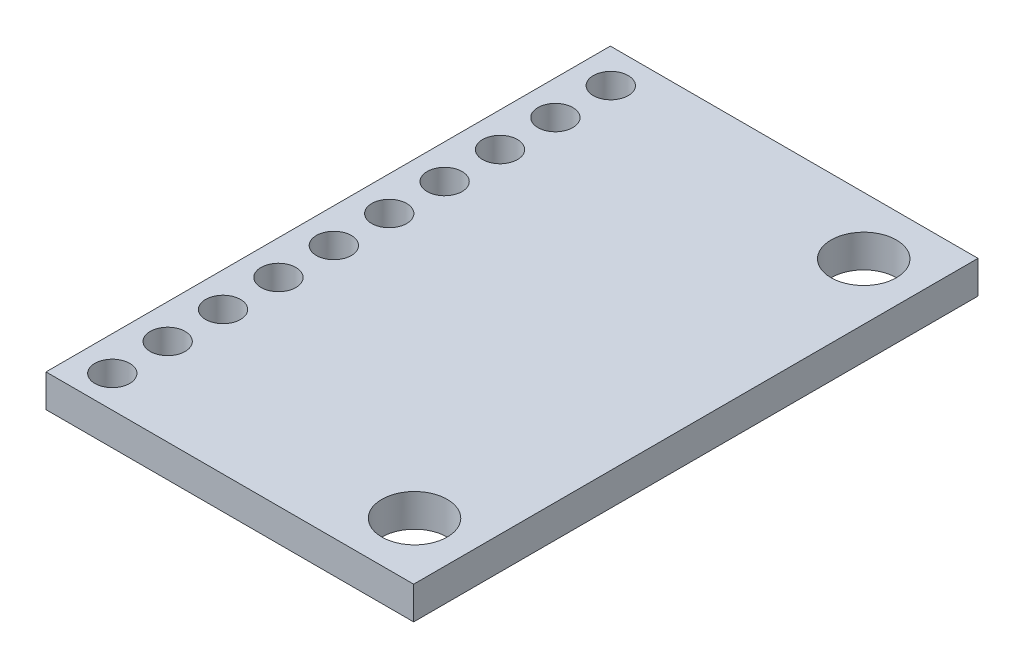
SolidWorks part; units mm, degrees
ref_plane "Front Plane" through (0, 0, 0) normal (0, 0, 1) x (1, 0, 0)
ref_plane "Top Plane" through (0, 0, 0) normal (0, 1, 0) x (1, 0, 0)
ref_plane "Right Plane" through (0, 0, 0) normal (1, 0, 0) x (0, 0, -1)
sketch "Sketch1" plane through (0, 0, 0) normal (0, 1, 0) x (1, 0, 0)
  line L1 (0, 0) -> (16.86, 0)
  line L2 (0, 0) -> (0, 25.88)
  line L3 (0, 25.88) -> (16.86, 25.88)
  line L4 (16.86, 0) -> (16.86, 25.88)
  dimension "D1" = 25.88
  dimension "D2" = 16.86
extrude "Boss-Extrude1" add sketch "Sketch1" along normal blind 1.5
sketch "Sketch2" plane through (0, 1.5, 0) normal (0, 1, 0) x (1, 0, 0)
  line L1 (16.86, 0) -> (16.86, 25.88) construction
  line L2 (0, 0) -> (16.86, 0) construction
  circle A0 centre (14.26, 23.24) radius 1.5
  circle A1 centre (14.26, 2.64) radius 1.5
  dimension "D1" = 3
  dimension "D2" = 20.6
  dimension "D3" = 2.6
  dimension "D4" = 2.64
extrude "Cut-Extrude1" cut sketch "Sketch2" against normal up to next
sketch "Sketch3" plane through (0, 1.5, 0) normal (0, 1, 0) x (1, 0, 0)
  line L0 (16.86, 25.88) -> (0, 25.88) construction
  line L1 (0, 25.88) -> (0, 0) construction
  circle A0 centre (1.58, 24.32) radius 0.8
  circle A1 centre (1.58, 21.78) radius 0.8
  circle A2 centre (1.58, 19.24) radius 0.8
  circle A3 centre (1.58, 16.7) radius 0.8
  circle A4 centre (1.58, 14.16) radius 0.8
  circle A5 centre (1.58, 11.62) radius 0.8
  circle A6 centre (1.58, 9.08) radius 0.8
  circle A7 centre (1.58, 6.54) radius 0.8
  circle A8 centre (1.58, 4) radius 0.8
  circle A9 centre (1.58, 1.46) radius 0.8
  dimension "D1" = 1.6
  dimension "D2" = 1.56
  dimension "D3" = 1.58
  dimension "D4" = 10
extrude "Cut-Extrude2" cut sketch "Sketch3" against normal up to next
